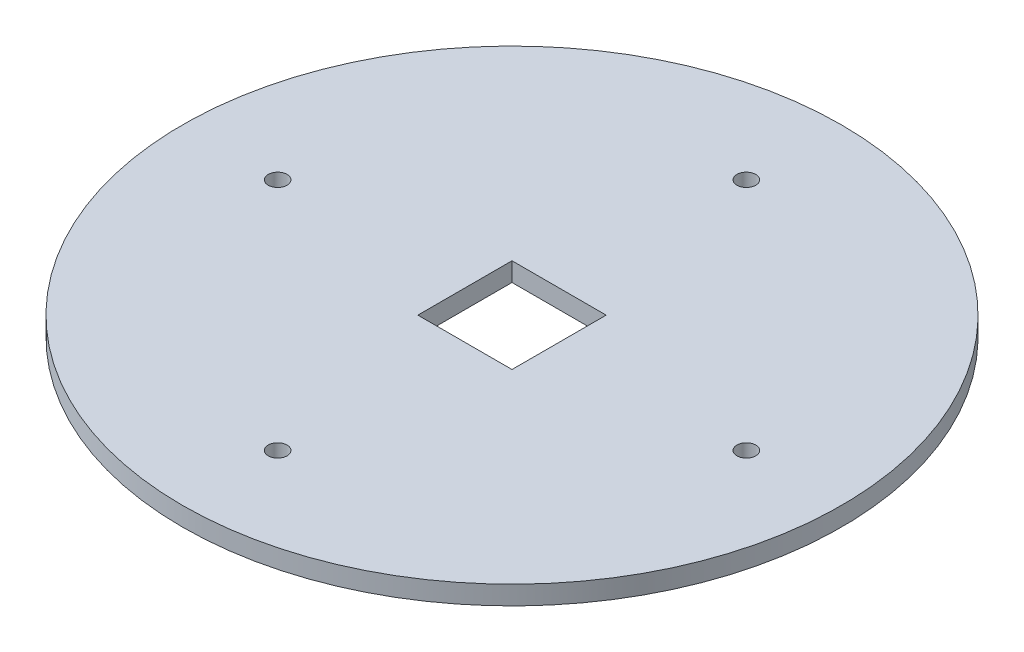
SolidWorks part; units mm, degrees
ref_plane "Front Plane" through (0, 0, 0) normal (0, 0, 1) x (1, 0, 0)
ref_plane "Top Plane" through (0, 0, 0) normal (0, 1, 0) x (1, 0, 0)
ref_plane "Right Plane" through (0, 0, 0) normal (1, 0, 0) x (0, 0, -1)
sketch "Sketch1" plane through (0, 0, 0) normal (0, 1, 0) x (1, 0, 0)
  line L1 (-5, 5) -> (5, 5)
  line L2 (-5, 5) -> (-5, -5)
  line L3 (-5, -5) -> (5, -5)
  line L4 (5, 5) -> (5, -5)
  line L5 (-5, 5) -> (5, -5) construction
  line L6 (-5, -5) -> (5, 5) construction
  circle A0 centre (0, 0) radius 35
  circle A1 centre (0, 0) radius 24.89 construction
  circle A2 centre (0, 24.89) radius 1
  circle A3 centre (24.89, 0) radius 1
  circle A4 centre (0, -24.89) radius 1
  circle A5 centre (-24.89, 0) radius 1
  point P15 (0, 0)
  dimension "D1" = 70
  dimension "D2" = 49.78
  dimension "D3" = 2
  dimension "D5" = 10
  dimension "D4" = 4
extrude "Boss-Extrude1" add sketch "Sketch1" along normal blind 2
